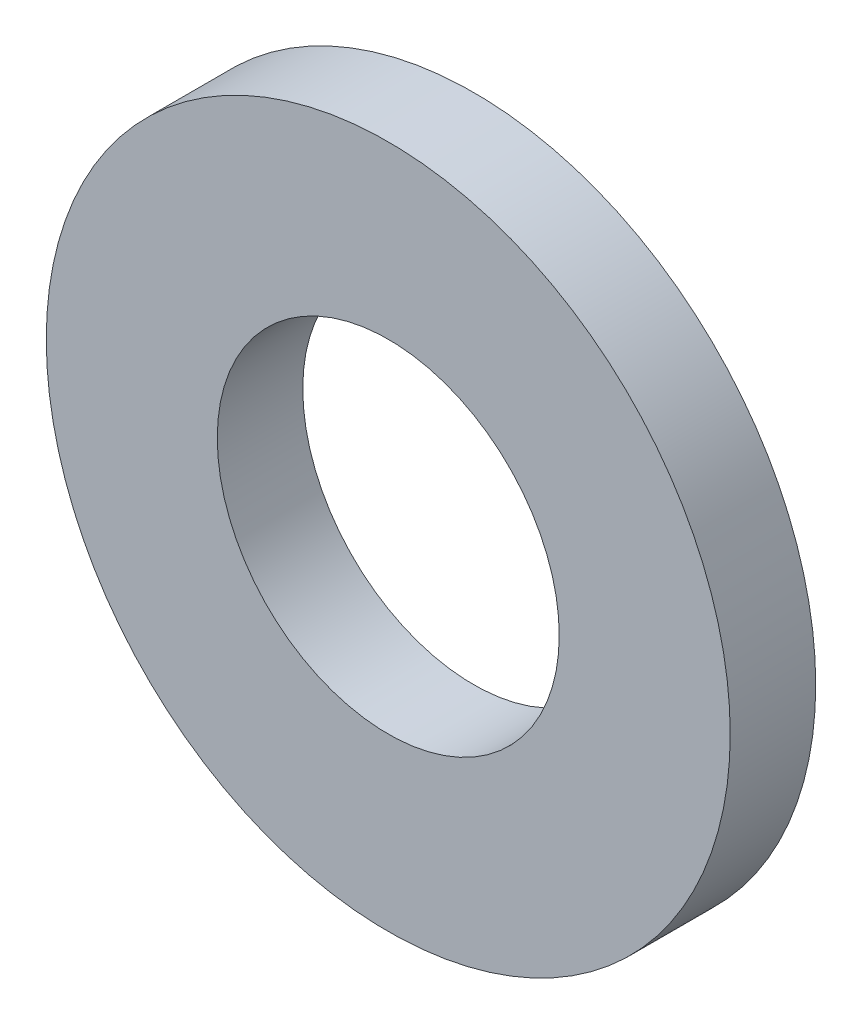
SolidWorks part; units mm, degrees
ref_plane "Front Plane" through (0, 0, 0) normal (0, 0, 1) x (1, 0, 0)
ref_plane "Top Plane" through (0, 0, 0) normal (0, 1, 0) x (1, 0, 0)
ref_plane "Right Plane" through (0, 0, 0) normal (1, 0, 0) x (0, 0, -1)
sketch "스케치1" plane through (0, 0, 0) normal (0, 0, 1) x (1, 0, 0)
  circle A0 centre (0, 0) radius 4
  circle A1 centre (0, 0) radius 2
extrude "보스-돌출1" add sketch "스케치1" along normal blind 1
